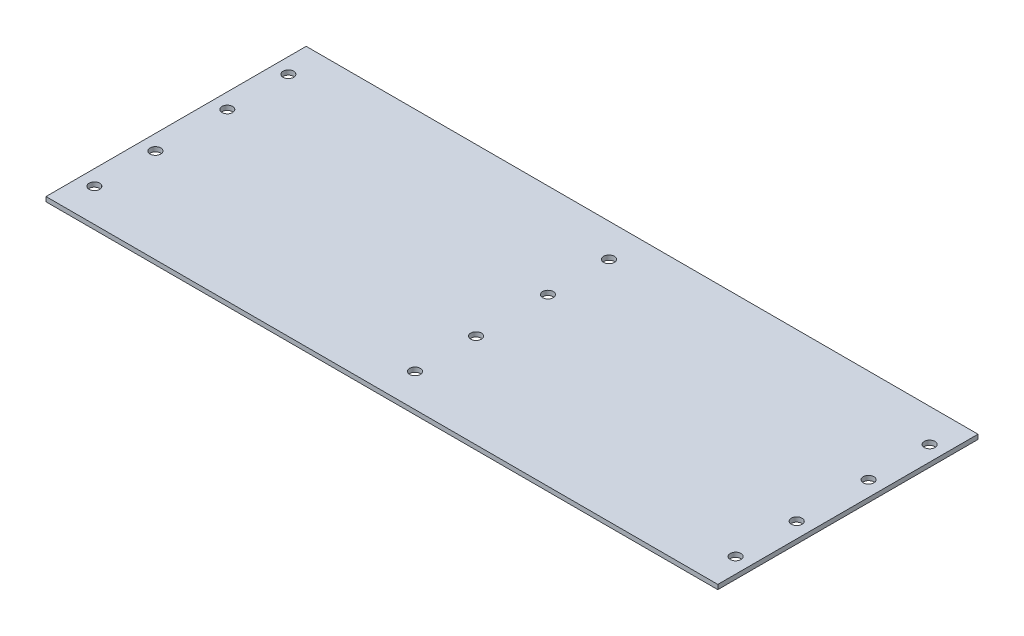
SolidWorks part; units mm, degrees
ref_plane "前视基准面" through (0, 0, 0) normal (0, 0, 1) x (1, 0, 0)
ref_plane "上视基准面" through (0, 0, 0) normal (0, 1, 0) x (1, 0, 0)
ref_plane "右视基准面" through (0, 0, 0) normal (1, 0, 0) x (0, 0, -1)
sketch "草图1" plane through (0, 0, 0) normal (0, 1, 0) x (1, 0, 0)
  line L1 (-65.705, 44.3173) -> (154.295, 44.3173)
  line L2 (-65.705, 44.3173) -> (-65.705, -40.8827)
  line L3 (-65.705, -40.8827) -> (154.295, -40.8827)
  line L4 (154.295, 44.3173) -> (154.295, -40.8827)
  dimension "D1" = 85.2
  dimension "D2" = 220
extrude "凸台-拉伸1" add sketch "草图1" along normal blind 1.5
sketch "草图2" plane through (0, 1.5, 0) normal (0, 1, 0) x (1, 0, 0)
  line L0 (-65.705, -40.8827) -> (154.295, -40.8827) construction
  line L1 (154.295, -40.8827) -> (154.295, 44.3173) construction
  line L2 (-65.705, 1.7173) -> (154.295, 1.7173)
  line L3 (-65.705, 44.3173) -> (-65.705, -40.8827) construction
  circle A0 centre (149.295, -30.0527) radius 1.75
  circle A1 centre (44.295, -30.0527) radius 1.75
  circle A2 centre (-60.705, -30.0527) radius 1.75
  circle A3 centre (44.295, -10.0527) radius 1.75
  circle A4 centre (-60.705, -10.0527) radius 1.75
  circle A5 centre (149.295, -10.0527) radius 1.75
  circle A6 centre (149.295, 13.4873) radius 1.75
  circle A7 centre (-60.705, 13.4873) radius 1.75
  circle A8 centre (44.295, 13.4873) radius 1.75
  circle A9 centre (-60.705, 33.4873) radius 1.75
  circle A10 centre (44.295, 33.4873) radius 1.75
  circle A11 centre (149.295, 33.4873) radius 1.75
  dimension "D2" = 5
  dimension "D3" = 3.5
  dimension "D1" = 10.83
  dimension "D4" = 3
  dimension "D5" = 2
extrude "切除-拉伸1" cut sketch "草图2" against normal blind 10 contours A0 | A5 | A3 | A1 | A8 | A10 | A6 | A11 | A9 | A7 | A4 | A2
